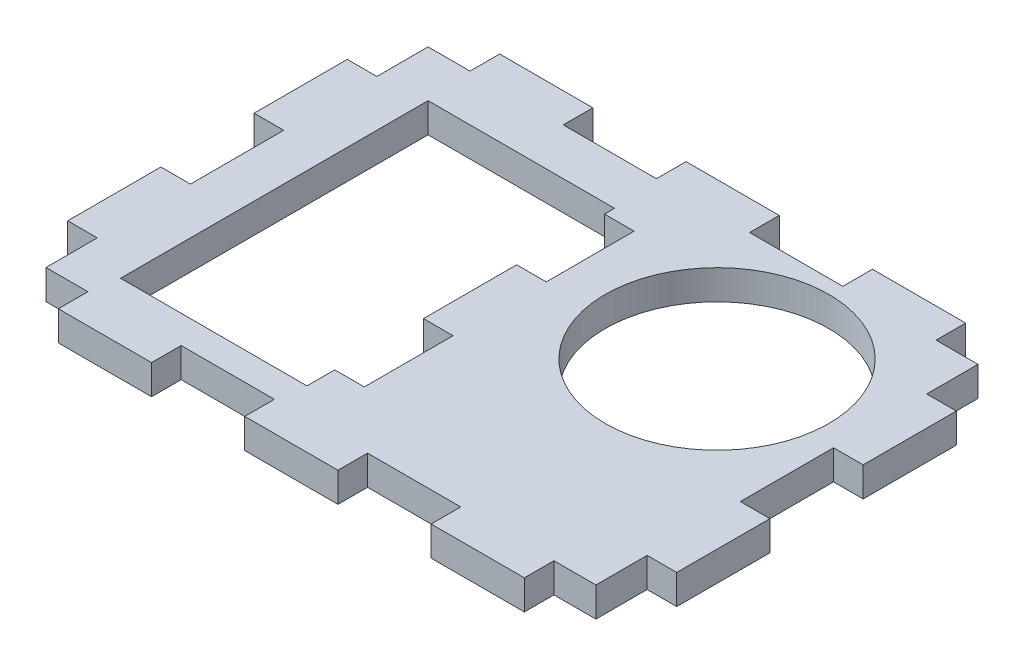
SolidWorks part; units mm, degrees
ref_plane "Front Plane" through (0, 0, 0) normal (0, 0, 1) x (1, 0, 0)
ref_plane "Top Plane" through (0, 0, 0) normal (0, 1, 0) x (1, 0, 0)
ref_plane "Right Plane" through (0, 0, 0) normal (1, 0, 0) x (0, 0, -1)
sketch "Sketch1" plane through (0, 0, 0) normal (0, 1, 0) x (1, 0, 0)
  line L1 (0, 0) -> (65.35, 0)
  line L2 (0, 0) -> (0, 47.35)
  line L3 (0, 47.35) -> (65.35, 47.35)
  line L4 (65.35, 0) -> (65.35, 47.35)
  line L5 (8.175, 6.175) -> (28.175, 6.175)
  line L6 (8.175, 6.175) -> (8.175, 39.175)
  line L7 (8.175, 39.175) -> (28.175, 39.175)
  line L8 (28.175, 6.175) -> (28.175, 39.175)
  circle A0 centre (47.675, 30.675) radius 12
  dimension "D7" = 24
  dimension "D1" = 47.35
  dimension "D2" = 65.35
  dimension "D3" = 8.175
  dimension "D4" = 6.175
  dimension "D5" = 8.175
  dimension "D6" = 20
  dimension "D8" = 17.675
  dimension "D9" = 16.675
extrude "Boss-Extrude1" add sketch "Sketch1" along normal blind 3.175
sketch "Sketch2" plane through (0, 3.175, 0) normal (0, 1, 0) x (1, 0, 0)
  line L0 (0, 47.35) -> (0, 0) construction
  line L1 (3.175, 8.675) -> (0, 8.675)
  line L2 (3.175, 8.675) -> (3.175, 0)
  line L3 (3.175, 0) -> (0, 0)
  line L4 (0, 8.675) -> (0, 0)
  line L5 (28.175, 6.175) -> (28.175, 39.175) construction
  line L6 (3.175, 18.675) -> (0, 18.675)
  line L7 (3.175, 18.675) -> (3.175, 28.675)
  line L8 (3.175, 28.675) -> (0, 28.675)
  line L9 (0, 18.675) -> (0, 28.675)
  line L10 (3.175, 38.675) -> (0, 38.675)
  line L11 (3.175, 38.675) -> (3.175, 47.35)
  line L12 (3.175, 47.35) -> (0, 47.35)
  line L13 (0, 38.675) -> (0, 47.35)
  line L14 (65.35, 47.35) -> (0, 47.35) construction
  line L15 (62.175, 38.675) -> (65.35, 38.675)
  line L16 (62.175, 38.675) -> (62.175, 47.35)
  line L17 (62.175, 47.35) -> (65.35, 47.35)
  line L18 (65.35, 38.675) -> (65.35, 47.35)
  line L19 (65.35, 0) -> (65.35, 47.35) construction
  line L20 (0, 0) -> (65.35, 0) construction
  line L21 (62.175, 28.675) -> (65.35, 28.675)
  line L22 (62.175, 28.675) -> (62.175, 18.675)
  line L23 (62.175, 18.675) -> (65.35, 18.675)
  line L24 (65.35, 28.675) -> (65.35, 18.675)
  line L25 (62.175, 8.675) -> (65.35, 8.675)
  line L26 (62.175, 8.675) -> (62.175, 0)
  line L27 (62.175, 0) -> (65.35, 0)
  line L28 (65.35, 8.675) -> (65.35, 0)
  line L29 (57.675, 3.175) -> (62.175, 3.175)
  line L30 (57.675, 3.175) -> (57.675, 0)
  line L31 (57.675, 0) -> (62.175, 0)
  line L32 (62.175, 3.175) -> (62.175, 0)
  line L33 (7.675, 3.175) -> (3.175, 3.175)
  line L34 (7.675, 3.175) -> (7.675, 0)
  line L35 (7.675, 0) -> (3.175, 0)
  line L36 (3.175, 3.175) -> (3.175, 0)
  line L37 (17.675, 3.175) -> (27.675, 3.175)
  line L38 (17.675, 3.175) -> (17.675, 0)
  line L39 (17.675, 0) -> (27.675, 0)
  line L40 (27.675, 3.175) -> (27.675, 0)
  line L41 (65.35, 47.35) -> (0, 47.35) construction
  line L42 (37.675, 3.175) -> (47.675, 3.175)
  line L43 (37.675, 3.175) -> (37.675, 0)
  line L44 (37.675, 0) -> (47.675, 0)
  line L45 (47.675, 3.175) -> (47.675, 0)
  line L46 (47.675, 44.175) -> (37.675, 44.175)
  line L47 (47.675, 44.175) -> (47.675, 47.35)
  line L48 (47.675, 47.35) -> (37.675, 47.35)
  line L49 (37.675, 44.175) -> (37.675, 47.35)
  line L50 (57.675, 44.175) -> (62.175, 44.175)
  line L51 (57.675, 44.175) -> (57.675, 47.35)
  line L52 (57.675, 47.35) -> (62.175, 47.35)
  line L53 (62.175, 44.175) -> (62.175, 47.35)
  line L54 (27.675, 44.175) -> (17.675, 44.175)
  line L55 (27.675, 44.175) -> (27.675, 47.35)
  line L56 (27.675, 47.35) -> (17.675, 47.35)
  line L57 (17.675, 44.175) -> (17.675, 47.35)
  line L58 (7.675, 44.175) -> (0, 44.175)
  line L59 (7.675, 44.175) -> (7.675, 47.35)
  line L60 (7.675, 47.35) -> (0, 47.35)
  line L61 (0, 44.175) -> (0, 47.35)
  line L62 (31.35, 28.675) -> (28.175, 28.675)
  line L63 (31.35, 28.675) -> (31.35, 38.0993)
  line L64 (31.35, 38.0993) -> (28.175, 38.0993)
  line L65 (28.175, 28.675) -> (28.175, 38.0993)
  line L67 (31.35, 18.675) -> (28.175, 18.675)
  line L68 (31.35, 18.675) -> (31.35, 9.1506)
  line L69 (31.35, 9.1506) -> (28.175, 9.1506)
  line L70 (28.175, 18.675) -> (28.175, 9.1506)
  point P72 (63.7625, 18.675)
  line M1 (0, 47.35) -> (0, 0)
  line M2 (0, 0) -> (65.35, 0)
  line M3 (65.35, 0) -> (65.35, 47.35)
  line M4 (65.35, 47.35) -> (0, 47.35)
  line M7 (28.175, 39.175) -> (28.175, 6.175)
  dimension "D1" = 10
  dimension "D2" = 8.675
  dimension "D3" = 3.175
  dimension "D4" = 10
  dimension "D5" = 10
  dimension "D6" = 3.175
  dimension "D7" = 10
  dimension "D8" = 10
  dimension "D9" = 10
  dimension "D10" = 4.5
  dimension "D11" = 10
extrude "Cut-Extrude1" cut sketch "Sketch2" against normal blind 3.175 contours L57 L54 L55 M4 | L49 L46 L47 M4 | L51 L50 L16 M4 | L16 L15 M3 M4 | L22 L23 L21 M3 | L25 L26 M2 M3 | L29 L30 L26 M2 | L45 L42 L43 M2 | L40 L37 L38 M2 | L34 L33 L2 M2 | L2 L1 M1 M2 | L7 L8 L6 M1 | L11 L58 L13 L10 | L58 L59 L11 M4 | L58 L11 M4 M1 | L63 L64 L62 M7 | L69 L68 L67 M7
